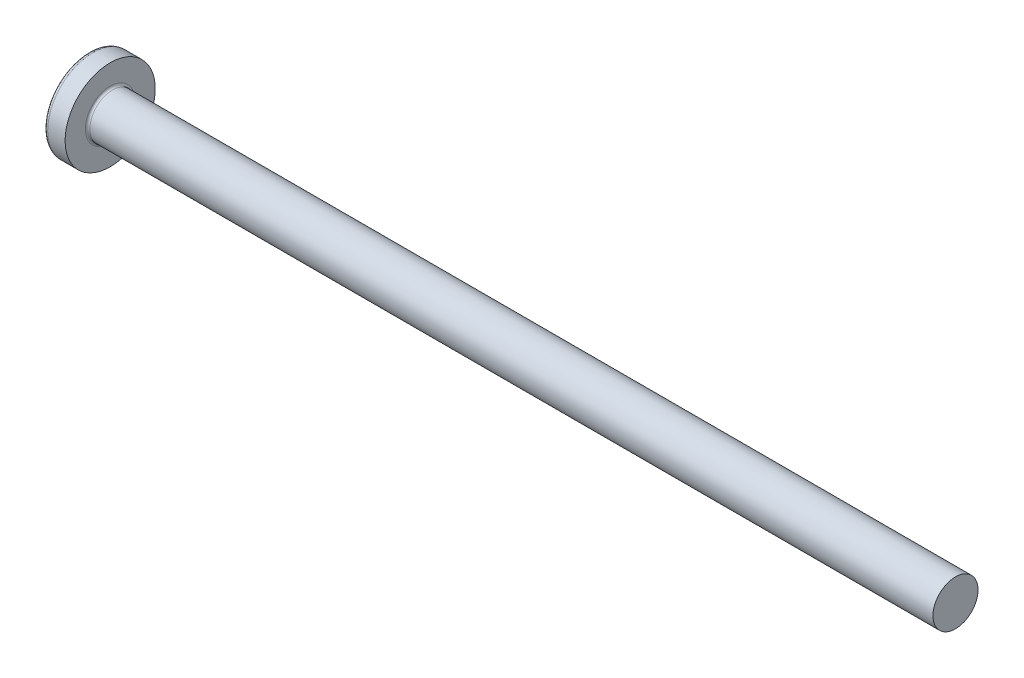
SolidWorks part; units mm, degrees
ref_plane "Plane1" through (0, 0, 0) normal (0, 0, 1) x (1, 0, 0)
ref_plane "Plane2" through (0, 0, 0) normal (0, 1, 0) x (1, 0, 0)
ref_plane "Plane3" through (0, 0, 0) normal (1, 0, 0) x (0, 0, -1)
sketch "BodySke" plane through (0, 0, 0) normal (0, 0, 1) x (1, 0, 0)
  line L0 (3.1, 2) -> (3.1, 4)
  line L1 (3.45, 6.35) -> (3.45, -3.175) construction
  line L2 (-25.4, 0) -> (127, 0) construction
  line L3 (78.1, 0) -> (0, 0)
  line L4 (3.1, 2) -> (78.1, 2)
  line L5 (78.1, 2) -> (78.1, 0)
  line L6 (1.5553, 4) -> (3.1, 4)
  line L8 (3.1, 6.35) -> (3.1, -3.175) construction
  arc A0 (1.2654, 3.8534) -> (0, 0) centre (6.5, 0) ccw
  arc A2 (1.2654, 3.8534) -> (1.5553, 4) centre (1.5553, 3.64) cw
  dimension "Head_crown_rad" = 6.5
  dimension "Head_fillet_rad" = 0.36
  dimension "Length" = 75
  dimension "Head_ht" = 3.1
  dimension "Head_dia" = 8
  dimension "Advance" = 0.7
  dimension "Thread_nom" = 75
  dimension "Diameter" = 4
revolve "Base-Revolve" add sketch "BodySke"
cosmetic thread "ThreadCosmetic" [suppressed]
fillet "Fillet1" radius 0.2 1 edges at (3.1, 0, 2)
sketch "Sketch3" plane through (0, 0, 0) normal (1, 0, 0) x (0, 0, -1)
  line L0 (0.515, -2.15) -> (-0.515, -2.15)
  line L1 (0.515, -2.15) -> (0.515, 2.15)
  line L2 (-0.515, 2.15) -> (0.515, 2.15)
  line L3 (-0.515, 2.15) -> (-0.515, -2.15)
  dimension "Cross_dia" = 4.3
  dimension "D1" = 2.15
  dimension "Cross_width" = 1.03
  dimension "D2" = 0.515
ref_plane "Plane4" through (2.34, 0, 0) normal (1, 0, 0) x (0, 0, -1)
sketch "Sketch4" plane through (2.34, 0, 0) normal (1, 0, 0) x (0, 0, -1)
  line L0 (0.515, -0.9833) -> (-0.515, -0.9833)
  line L1 (0.515, -0.9833) -> (0.515, 0.9833)
  line L2 (-0.515, 0.9833) -> (0.515, 0.9833)
  line L3 (-0.515, 0.9833) -> (-0.515, -0.9833)
  dimension "D1" = 1.03
  dimension "D2" = 1.9666
  dimension "D3" = 0.515
  dimension "D4" = 0.9833
loft "Recess" cut profiles "Sketch3", "Sketch4"
pattern_circular "RecPat" count 2 every 90 about axis through (0, 0, 0) along (1, 0, 0) of "Recess"
sketch "RecCorSke" plane through (0, 0, 0) normal (0, 0, 1) x (1, 0, 0)
  line L0 (-3.175, 0) -> (15.875, 0) construction
  line L1 (-25.4, 0) -> (127, 0) construction
  line L2 (0, 0) -> (0, 1.0146)
  line L3 (0, 1.0146) -> (2.34, 0.851)
  line L4 (2.34, 0.851) -> (2.6165, 0)
  line L5 (2.6165, 0) -> (0, 0)
  dimension "Diameter" = 1.702
  dimension "Depth" = 2.34
  dimension "Draft_angle" = 4
  dimension "Bottom_angle" = 18
revolve "RecessCore" cut sketch "RecCorSke" angle 360 about L0
sketch "ThdSchSke" plane through (0, 0, 0) normal (0, 0, 1) x (1, 0, 0)
  line L0 (4.5, -1.61) -> (4.2269, -2)
  line L1 (4.5, -1.61) -> (4.7731, -2)
  line L2 (4.7731, -2) -> (4.7731, -2.5)
  line L3 (-3.175, 0) -> (5.1513, 0) construction
  line L5 (4.7731, -2.5) -> (4.2269, -2.5)
  line L6 (4.2269, -2.5) -> (4.2269, -2)
  dimension "Diameter" = 4
  dimension "SideAngle" = 55
  dimension "VeeAngle" = 70
  dimension "Thread_minor" = 3.22
  dimension "Overcut" = 5
  dimension "Start" = 4.5
revolve "ThreadSchematic" [suppressed] cut sketch "ThdSchSke" angle 360 about L3
pattern_linear "ThdSchPat" [suppressed]
equation "\"D1@Sketch3\" = \"Cross_dia@Sketch3\" / 2"
equation "\"D2@Sketch3\" = \"Cross_width@Sketch3\" / 2"
equation "\"Depth@RecCorSke\" = \"Cross_depth@Plane4\""
equation "\"D1@Sketch4\" = \"Cross_width@Sketch3\""
equation "\"D2@Sketch4\" = \"Cross_dia@Sketch3\" - 2.0 * \"Cross_depth@Plane4\" * tan(26.5  * 0.017453292)"
equation "\"D3@Sketch4\" = \"D1@Sketch4\" / 2"
equation "\"D4@Sketch4\" = \"D2@Sketch4\" / 2"
equation "\"Thread_length@ThreadCosmetic\" = ((sgn( (\"Length@BodySke\" - \"Advance@BodySke\" * 2.0 ) - \"Thread_nom@BodySke\" )-1)*( (\"Length@BodySke\" - \"Advance@BodySke\" * 2.0 ) - \"Thread_nom@BodySke\" ))/-2+ \"Thread_nom@BodySke\""
equation "\"Thread_minor@ThdSchSke\" = \"Thread_minor@ThreadCosmetic\""
equation "\"Diameter@ThdSchSke\" = \"Diameter@BodySke\""
equation "\"Overcut@ThdSchSke\" = \"Diameter@BodySke\" * 1.25"
equation "\"Start@ThdSchSke\" = \"Head_ht@BodySke\" + \"Length@BodySke\" - \"Thread_length@ThreadCosmetic\"  '---Non-countersunk---"
equation "\"Num_threads@ThdSchPat\" = int( \"Thread_length@ThreadCosmetic\" / \"Advance@BodySke\" + 0.999 )  + 1"
equation "\"Advance@ThdSchPat\" = \"Thread_length@ThreadCosmetic\" /  (\"Num_threads@ThdSchPat\" - 1) 'relax it"
